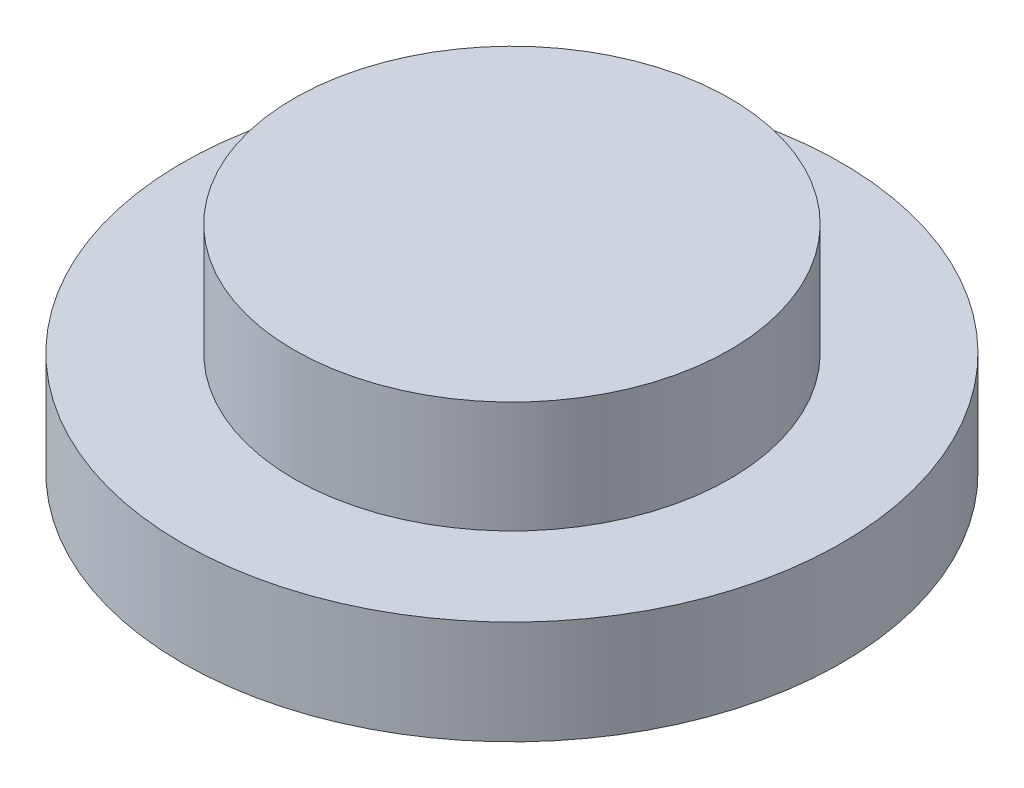
SolidWorks part; units mm, degrees
ref_plane "Front Plane" through (0, 0, 0) normal (0, 0, 1) x (1, 0, 0)
ref_plane "Top Plane" through (0, 0, 0) normal (0, 1, 0) x (1, 0, 0)
ref_plane "Right Plane" through (0, 0, 0) normal (1, 0, 0) x (0, 0, -1)
sketch "Sketch1" plane through (0, 0, 0) normal (0, 1, 0) x (1, 0, 0)
  circle A0 centre (0, 0) radius 9.525
  dimension "D1" = 19.05
extrude "Boss-Extrude1" add sketch "Sketch1" along normal blind 2.9972
sketch "Sketch2" plane through (0, 2.9972, 0) normal (0, 1, 0) x (1, 0, 0)
  circle A0 centre (0, 0) radius 6.2992
  dimension "D1" = 12.5984
extrude "Boss-Extrude2" add sketch "Sketch2" along normal blind 3.2258
